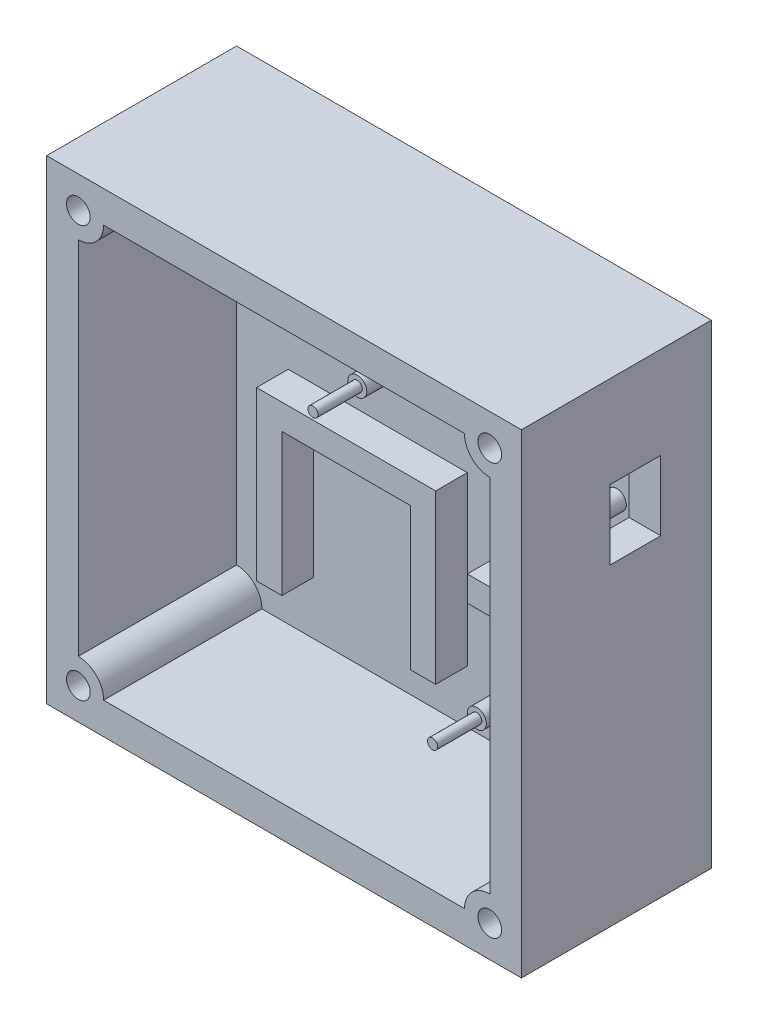
SolidWorks part; units mm, degrees
ref_plane "Front Plane" through (0, 0, 0) normal (0, 0, 1) x (1, 0, 0)
ref_plane "Top Plane" through (0, 0, 0) normal (0, 1, 0) x (1, 0, 0)
ref_plane "Right Plane" through (0, 0, 0) normal (1, 0, 0) x (0, 0, -1)
sketch "Sketch1" plane through (0, 0, 0) normal (0, 0, 1) x (1, 0, 0)
  line L1 (-47.625, -47.625) -> (47.625, -47.625)
  line L2 (-47.625, -47.625) -> (-47.625, 47.625)
  line L3 (-47.625, 47.625) -> (47.625, 47.625)
  line L4 (47.625, -47.625) -> (47.625, 47.625)
  line L5 (-47.625, -47.625) -> (47.625, 47.625) construction
  line L6 (-47.625, 47.625) -> (47.625, -47.625) construction
  point P0 (0, 0)
  dimension "D1" = 95.25
  dimension "D2" = 95.25
extrude "Boss-Extrude1" add sketch "Sketch1" along normal blind 38.1
shell "Shell1" thickness 6.35
ref_plane "Plane1" through (0, 0, 38.1) normal (0, 0, 1) x (1, 0, 0)
sketch "Sketch2" plane through (0, 0, 38.1) normal (0, 0, 1) x (1, 0, 0)
  line L0 (41.275, 41.275) -> (-41.275, 41.275) construction
  line L1 (-41.275, 41.275) -> (-41.275, -41.275) construction
  line L2 (-41.275, 41.275) -> (-36.195, 41.275)
  line L3 (-41.275, 41.275) -> (-41.275, 36.195)
  line L4 (41.275, 41.275) -> (-41.275, 41.275) construction
  line L5 (41.275, -41.275) -> (41.275, 41.275) construction
  line L6 (36.195, 41.275) -> (41.275, 41.275)
  line L7 (41.275, 41.275) -> (41.275, 36.195)
  line L8 (-41.275, -41.275) -> (41.275, -41.275) construction
  line L9 (41.275, -36.195) -> (41.275, -41.275)
  line L10 (41.275, -41.275) -> (36.195, -41.275)
  line L11 (-41.275, -41.275) -> (41.275, -41.275) construction
  line L12 (-41.275, -36.195) -> (-41.275, -41.275)
  line L13 (-41.275, -41.275) -> (-36.195, -41.275)
  arc A0 (-36.195, 41.275) -> (-41.275, 36.195) centre (-41.275, 41.275) cw
  arc A1 (36.195, 41.275) -> (41.275, 36.195) centre (41.275, 41.275) ccw
  arc A2 (41.275, -36.195) -> (36.195, -41.275) centre (41.275, -41.275) ccw
  arc A3 (-41.275, -36.195) -> (-36.195, -41.275) centre (-41.275, -41.275) cw
  dimension "D1" = 5.08
extrude "Boss-Extrude2" add sketch "Sketch2" against normal up to surface (31.75 mm away) up to face at (0, 0, 6.35)
sketch "Sketch3" plane through (0, 0, 6.35) normal (0, 0, 1) x (1, 0, 0)
  line L0 (41.275, -36.195) -> (41.275, 36.195) construction
  circle A0 centre (35.0157, 31.115) radius 1.905
  circle A1 centre (-10.7043, 31.115) radius 1.016
  circle A2 centre (-10.7043, 13.335) radius 1.905
  circle A3 centre (35.0157, 13.335) radius 1.905
  dimension "D1" = 3.81
  dimension "D2" = 2.032
  dimension "D3" = 6.2593
  dimension "D4" = 17.78
  dimension "D5" = 45.72
  dimension "D6" = 10.16
extrude "Boss-Extrude3" add sketch "Sketch3" along normal blind 6.35
ref_plane "Plane2" through (0, 0, 12.7) normal (0, 0, 1) x (1, 0, 0)
sketch "Sketch4" plane through (0, 0, 12.7) normal (0, 0, 1) x (1, 0, 0)
  circle A0 centre (-10.7043, 31.115) radius 1.016
  circle A1 centre (-10.7043, 13.335) radius 1.016
  circle A2 centre (35.0157, 31.115) radius 1.016
  circle A3 centre (35.0157, 13.335) radius 1.016
  dimension "D1" = 2.032
extrude "Boss-Extrude4" add sketch "Sketch4" along normal blind 8.89
ref_plane "Plane3" through (0, 0, 6.35) normal (0, 0, 1) x (1, 0, 0)
sketch "Sketch5" plane through (0, 0, 6.35) normal (0, 0, 1) x (1, 0, 0)
  line L0 (-36.195, -41.275) -> (36.195, -41.275) construction
  line L5 (11.3665, -13.335) -> (11.3665, -40.6427) construction
  line L6 (11.3665, -13.335) -> (33.655, -13.335)
  line L7 (11.3665, -13.335) -> (11.3665, -8.255)
  line L8 (11.3665, -8.255) -> (33.655, -8.255)
  line L9 (33.655, -13.335) -> (33.655, -8.255)
  line L10 (11.3665, -13.335) -> (33.655, -8.255) construction
  line L11 (11.3665, -8.255) -> (33.655, -13.335) construction
  line L12 (33.655, -13.335) -> (33.655, -28.5697) construction
  line L13 (41.275, -36.195) -> (41.275, 36.195) construction
  circle A0 centre (13.2715, -32.385) radius 1.905
  circle A1 centre (31.75, -32.385) radius 1.905
  point P4 (22.5108, -10.795)
  dimension "D4" = 3.81
  dimension "D3" = 18.4785
  dimension "D1" = 8.89
  dimension "D2" = 19.05
  dimension "D5" = 5.08
  dimension "D6" = 9.525
extrude "Boss-Extrude5" add sketch "Sketch5" along normal blind 6.35
ref_plane "Plane4" through (0, 0, 12.7) normal (0, 0, 1) x (1, 0, 0)
sketch "Sketch7" plane through (0, 0, 12.7) normal (0, 0, 1) x (1, 0, 0)
  circle A0 centre (13.2715, -32.385) radius 1.016
  circle A1 centre (31.75, -32.385) radius 1.016
  dimension "D1" = 2.032
extrude "Boss-Extrude6" add sketch "Sketch7" along normal blind 8.89
ref_plane "Plane5" through (0, 0, 38.1) normal (0, 0, 1) x (1, 0, 0)
sketch "Sketch8" plane through (0, 0, 38.1) normal (0, 0, 1) x (1, 0, 0)
  circle A0 centre (-41.275, 41.275) radius 2.3812
  circle A1 centre (41.275, 41.275) radius 2.3812
  circle A2 centre (41.275, -41.275) radius 2.3812
  circle A3 centre (-41.275, -41.275) radius 2.3812
  arc A4 (-36.195, -41.275) -> (-41.275, -36.195) centre (-41.275, -41.275) ccw construction
  arc A5 (-41.275, 36.195) -> (-36.195, 41.275) centre (-41.275, 41.275) ccw construction
  arc A6 (36.195, 41.275) -> (41.275, 36.195) centre (41.275, 41.275) ccw construction
  arc A7 (41.275, -36.195) -> (36.195, -41.275) centre (41.275, -41.275) ccw construction
  dimension "D1" = 4.7625
extrude "Cut-Extrude1" cut sketch "Sketch8" against normal blind 8.89
ref_plane "Plane7" through (0, 0, 6.35) normal (0, 0, 1) x (1, 0, 0)
sketch "Sketch10" plane through (0, 0, 6.35) normal (0, 0, 1) x (1, 0, 0)
  line L0 (-30.8991, -30.607) -> (-30.8991, 2.9972)
  line L1 (-30.8991, 2.9972) -> (5.0165, 2.9972)
  line L2 (5.0165, 2.9972) -> (5.0165, -30.607)
  line L3 (5.0165, -30.607) -> (-0.0635, -30.607)
  line L4 (-0.0635, -30.607) -> (-0.0635, -2.0828)
  line L5 (-0.0635, -2.0828) -> (-25.8191, -2.0828)
  line L6 (-25.8191, -2.0828) -> (-25.8191, -30.607)
  line L7 (-25.8191, -30.607) -> (-30.8991, -30.607)
  line L8 (-36.195, -41.275) -> (36.195, -41.275) construction
  line L11 (11.3665, -8.255) -> (11.3665, -13.335) construction
  dimension "D1" = 5.08
  dimension "D2" = 25.7556
  dimension "D3" = 28.5242
  dimension "D4" = 5.08
  dimension "D5" = 10.668
  dimension "D6" = 6.35
extrude "Boss-Extrude7" add sketch "Sketch10" along normal blind 6.35
ref_plane "Plane8" through (47.625, 0, 0) normal (1, 0, 0) x (0, 0, -1)
sketch "Sketch12" plane through (47.625, 0, 0) normal (1, 0, 0) x (0, 0, -1)
  line L0 (-10.16, 29.21) -> (-10.16, 33.02) construction
  line L1 (-10.16, 15.24) -> (-20.32, 15.24)
  line L2 (-10.16, 15.24) -> (-10.16, 29.21)
  line L3 (-10.16, 29.21) -> (-20.32, 29.21)
  line L4 (-20.32, 15.24) -> (-20.32, 29.21)
  line L5 (-10.16, 15.24) -> (-20.32, 29.21) construction
  line L6 (-10.16, 29.21) -> (-20.32, 15.24) construction
  line L7 (-12.7, 15.24) -> (-12.7, 11.43) construction
  line L8 (-6.35, 33.02) -> (-12.7, 33.02) construction
  line L10 (-38.1, 47.625) -> (0, 47.625) construction
  point P0 (-15.24, 22.225)
  dimension "D1" = 10.16
  dimension "D2" = 13.97
  dimension "D3" = 2.54
  dimension "D4" = 25.4
extrude "Cut-Extrude2" cut sketch "Sketch12" against normal up to surface (6.35 mm away) contours L4 L3 L2 L1 up to face at (41.275, 0, 22.225)
